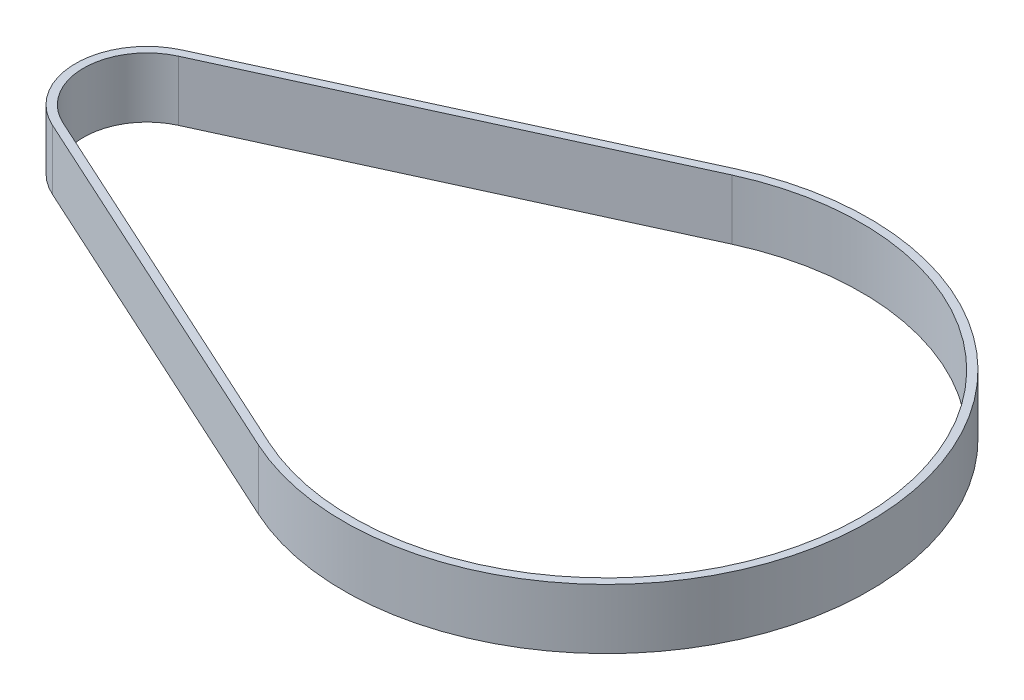
SolidWorks part; units mm, degrees
ref_plane "Front Plane" through (0, 0, 0) normal (0, 0, 1) x (1, 0, 0)
ref_plane "Top Plane" through (0, 0, 0) normal (0, 1, 0) x (1, 0, 0)
ref_plane "Right Plane" through (0, 0, 0) normal (1, 0, 0) x (0, 0, -1)
sketch "Sketch1" plane through (0, 0, 0) normal (0, 1, 0) x (1, 0, 0)
  line L0 (-48.6435, 5.7736) -> (-10.6158, 23.1852)
  line L1 (-48.6435, -5.7736) -> (-10.6158, -23.1852)
  line L2 (-48.9766, 6.501) -> (-10.9488, 23.9126)
  line L3 (-48.9766, -6.501) -> (-10.9488, -23.9126)
  arc A0 (-10.6158, -23.1852) -> (-10.6158, 23.1852) centre (0, 0) ccw
  arc A1 (-48.6435, 5.7736) -> (-48.6435, -5.7736) centre (-46, 0) ccw
  arc A2 (-10.9488, -23.9126) -> (-10.9488, 23.9126) centre (0, 0) ccw
  arc A3 (-48.9766, 6.501) -> (-48.9766, -6.501) centre (-46, 0) ccw
  dimension "D1" = 12.7
  dimension "D2" = 51
  dimension "D3" = 46
  dimension "D4" = 0.8
extrude "Boss-Extrude1" add sketch "Sketch1" along normal blind 6
